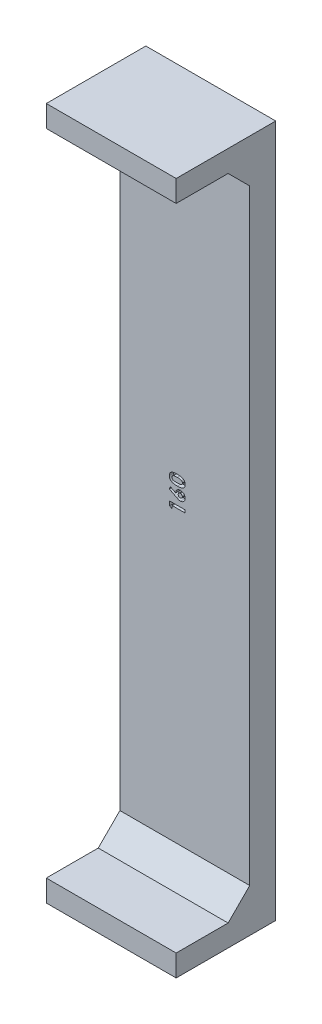
SolidWorks part; units mm, degrees
ref_plane "Front Plane" through (0, 0, 0) normal (0, 0, 1) x (1, 0, 0)
ref_plane "Top Plane" through (0, 0, 0) normal (0, 1, 0) x (1, 0, 0)
ref_plane "Right Plane" through (0, 0, 0) normal (1, 0, 0) x (0, 0, -1)
sketch "Sketch1" plane through (0, 0, 0) normal (0, 0, 1) x (1, 0, 0)
  line L1 (-15, 0) -> (15, 0)
  line L2 (-15, 0) -> (-15, 159.95)
  line L3 (-15, 159.95) -> (15, 159.95)
  line L4 (15, 0) -> (15, 159.95)
  point P4 (0, 0)
  dimension "D1" = 30
  dimension "D2" = 159.95
extrude "Boss-Extrude1" add sketch "Sketch1" along normal mid plane 6
sketch "Sketch2" plane through (0, 0, 0) normal (0, 0, 1) x (1, 0, 0)
  line L0 (15, 0) -> (15, 159.95) construction
  line L1 (-15, 0) -> (15, 0)
  line L2 (-15, 0) -> (-15, 5)
  line L3 (-15, 5) -> (15, 5)
  line L4 (15, 0) -> (15, 5)
  dimension "D1" = 5
extrude "Boss-Extrude2" add sketch "Sketch2" along normal blind 20
sketch "Sketch3" plane through (0, 0, 0) normal (0, 0, 1) x (1, 0, 0)
  line L0 (15, 5) -> (15, 159.95) construction
  line L1 (-15, 159.95) -> (15, 159.95)
  line L2 (-15, 159.95) -> (-15, 154.95)
  line L3 (-15, 154.95) -> (15, 154.95)
  line L4 (15, 159.95) -> (15, 154.95)
  dimension "D1" = 5
extrude "Boss-Extrude3" add sketch "Sketch3" along normal blind 20
chamfer "Chamfer1" distance 5 angle 45 2 edges at (0, 5, 3) (0, 154.95, 3)
sketch "Sketch4" plane through (0, 0, 3) normal (0, 0, 1) x (1, 0, 0)
  line L0 (0, 10) -> (0, 149.95) construction
  line L1 (-15, 10) -> (15, 10) construction
  line L2 (15, 149.95) -> (-15, 149.95) construction
  text T0 "<b>160</b>"
extrude "Cut-Extrude1" cut sketch "Sketch4" against normal blind 1
